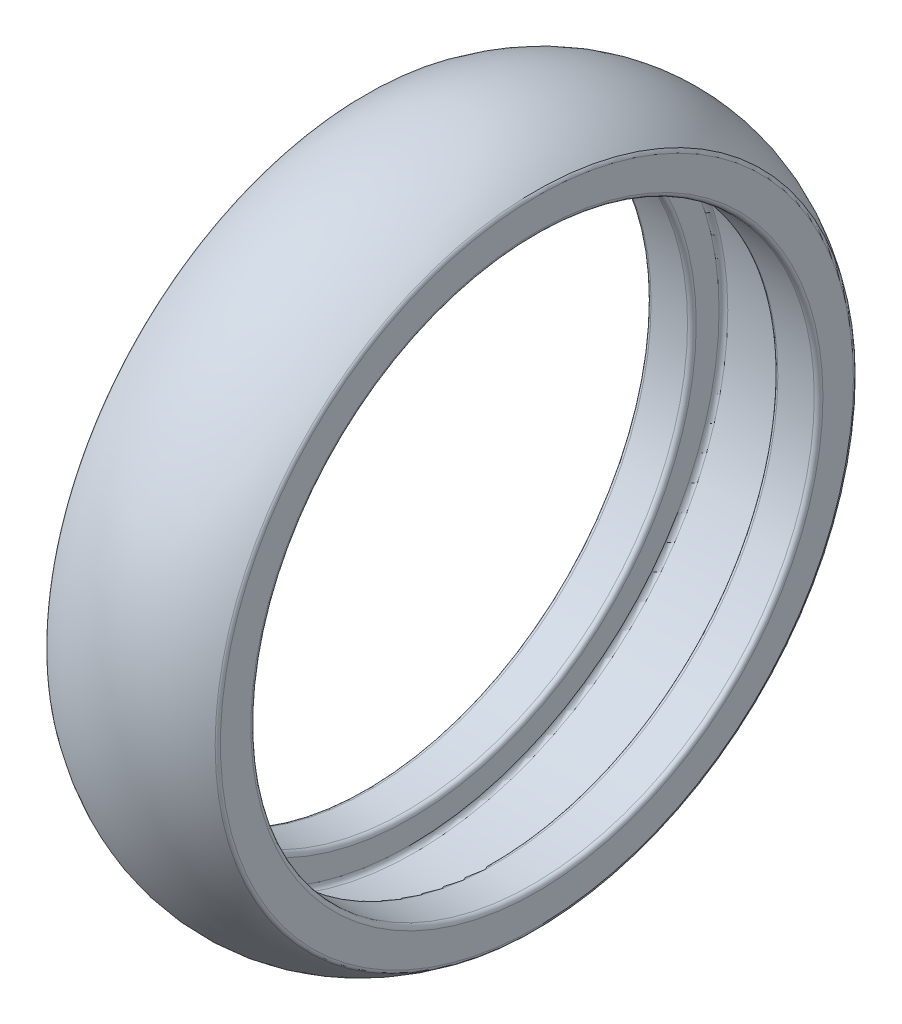
SolidWorks part; units mm, degrees
material "Силиконовая резина"
ref_plane "Front" through (0, 0, 0) normal (0, 0, 1) x (1, 0, 0)
ref_plane "Top" through (0, 0, 0) normal (0, 1, 0) x (1, 0, 0)
ref_plane "Right" through (0, 0, 0) normal (1, 0, 0) x (0, 0, -1)
sketch "Эскиз1" plane through (0, 0, 0) normal (0, 0, 1) x (1, 0, 0)
  line L1 (0, 0) -> (0, 42.5285) construction
  line L2 (-7.9, 25.9) -> (-7.9, 29.2999)
  line L3 (0, 31.95) -> (-45.6499, 31.95) construction
  line L5 (-3.75, 25.9) -> (-3.75, 28.8)
  line L6 (-3.75, 28.8) -> (3.75, 28.8)
  line L7 (3.75, 28.8) -> (3.75, 25.9)
  line L8 (-7.9, 25.9) -> (-3.75, 25.9)
  line L9 (7.9, 25.9) -> (7.9, 29.2999)
  line L10 (3.75, 25.9) -> (7.9, 25.9)
  line L11 (0, 0) -> (-14.8904, 0) construction
  arc A2 (7.9, 29.2999) -> (-7.9, 29.2999) centre (0, 18.85) ccw
  circle A3 centre (0, 0) radius 3.75 construction
  circle A4 centre (-7.9, 0) radius 25.9 construction
  point P10 (0, 31.95)
  point P12 (0, 31.95)
  point P15 (0, 0)
  dimension "D1" = 7.9
  dimension "D3" = 26.2
  dimension "D4" = 7.9
  dimension "D6" = 51.8
  dimension "D2" = 31.95
  dimension "D5" = 7.5
  dimension "D7" = 25.9
  dimension "D8" = 28.8
  dimension "D9" = 3.75
revolve "Повернуть1" add sketch "Эскиз1" angle 360 about L11
fillet "Скругление1" radius 0.4 8 edges at (3.75, 0, -25.9) (7.9, 0, -25.9) (-7.9, 0, -25.9) (-3.75, 0, -25.9) (-3.75, 0, -28.8) (3.75, 0, -28.8) (7.9, 0, -29.2999) (-7.9, 0, -29.2999)
